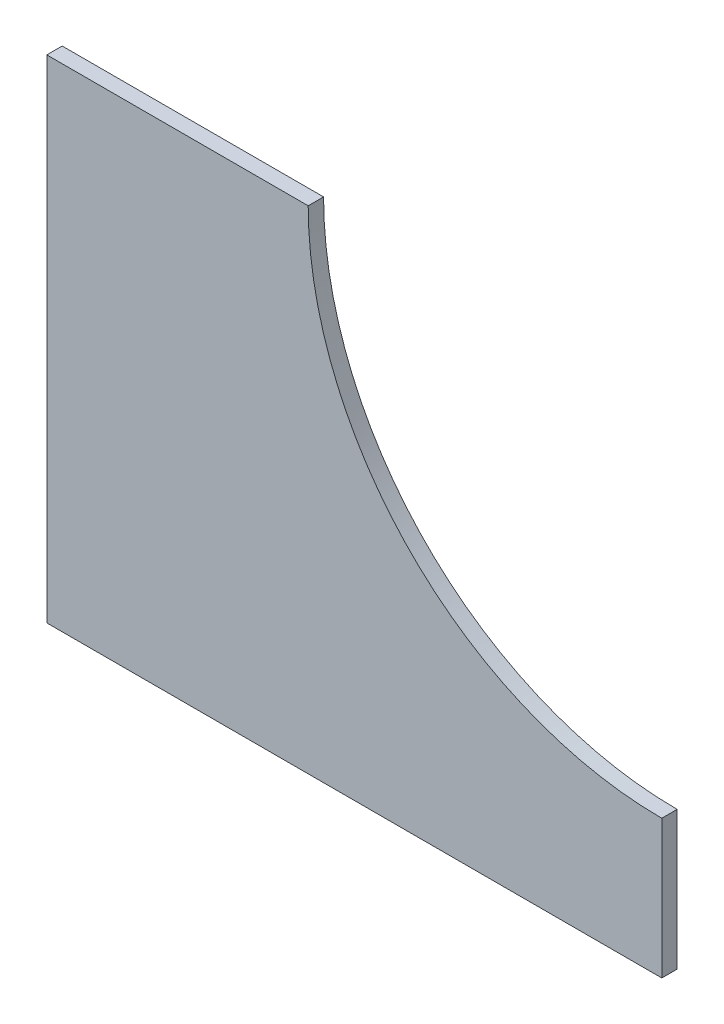
SolidWorks part; units mm, degrees
material "6061-T6 (SS)"
ref_plane "Front Plane" through (0, 0, 0) normal (0, 0, 1) x (1, 0, 0)
ref_plane "Top Plane" through (0, 0, 0) normal (0, 1, 0) x (1, 0, 0)
ref_plane "Right Plane" through (0, 0, 0) normal (1, 0, 0) x (0, 0, -1)
sketch "Sketch1" plane through (0, 0, 0) normal (0, 0, 1) x (1, 0, 0)
  line L0 (98.4295, -196.655) -> (98.4295, -225.23)
  line L1 (98.4295, -225.23) -> (-28.5705, -225.23)
  line L2 (-28.5705, -225.23) -> (-28.5705, -123.63)
  line L4 (-28.5705, -123.63) -> (25.4045, -123.63)
  line L5 (98.4295, -196.655) -> (73.0295, -196.655) construction
  arc A0 (98.4295, -196.655) -> (25.4045, -123.63) centre (98.4295, -123.63) cw
  point P3 (98.4295, -225.23)
  dimension "D4" = 73.025
  dimension "D1" = 101.6
  dimension "D2" = 28.575
  dimension "D3" = 127
  dimension "D5" = 25.4
extrude "Boss-Extrude1" add sketch "Sketch1" along normal blind 3.175
